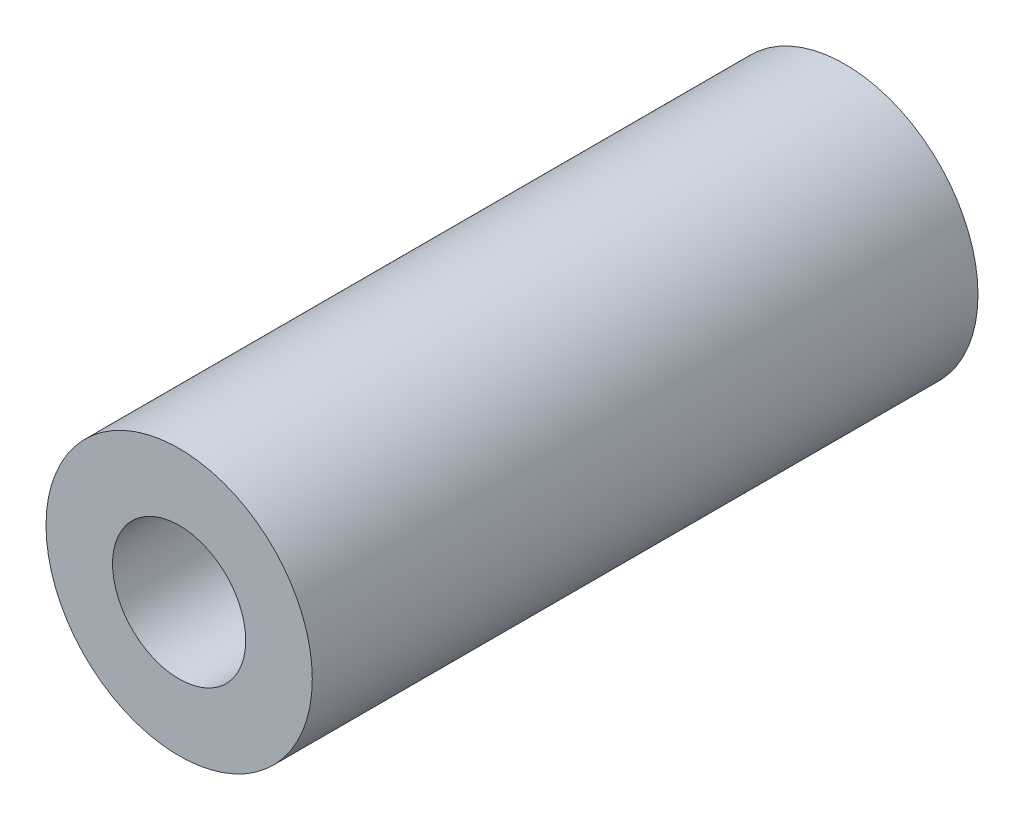
SolidWorks part; units mm, degrees
material "Delrin 2700 NC010, Low Viscosity Acetal Copolymer (SS)"
ref_plane "Front Plane" through (0, 0, 0) normal (0, 0, 1) x (1, 0, 0)
ref_plane "Top Plane" through (0, 0, 0) normal (0, 1, 0) x (1, 0, 0)
ref_plane "Right Plane" through (0, 0, 0) normal (1, 0, 0) x (0, 0, -1)
sketch "Sketch1" plane through (0, 0, 0) normal (0, 1, 0) x (1, 0, 0)
  line L0 (0, -25) -> (0, 25) construction
  line L1 (10, -25) -> (5, -25)
  line L2 (10, -25) -> (10, 25)
  line L3 (10, 25) -> (5, 25)
  line L4 (5, -25) -> (5, 25)
  line L5 (0, 25) -> (5, 25) construction
  line L6 (5, -25) -> (0, -25) construction
  line L7 (0, 0) -> (5, 0) construction
  dimension "D1" = 10
  dimension "D2" = 20
  dimension "D3" = 50
revolve "Revolve1" add sketch "Sketch1" angle 360 about L0
cosmetic thread "Cosmetic Thread1" parameters "D2"=12
